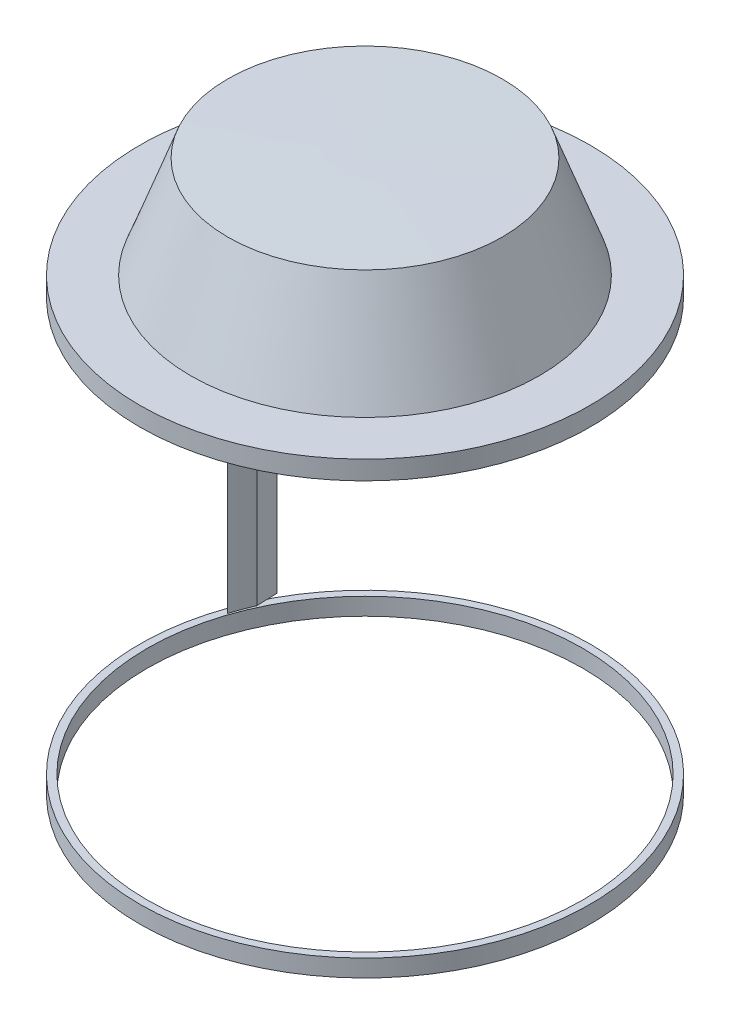
SolidWorks part; units mm, degrees
ref_plane "Alzado" through (0, 0, 0) normal (0, 0, 1) x (1, 0, 0)
ref_plane "Planta" through (0, 0, 0) normal (0, 1, 0) x (1, 0, 0)
ref_plane "Vista lateral" through (0, 0, 0) normal (1, 0, 0) x (0, 0, -1)
sketch "Croquis1" plane through (0, 0, 0) normal (0, 0, 1) x (1, 0, 0)
  line L0 (0, 38.8006) -> (0, -62.5731)
  line L1 (0, -62.5731) -> (50.8215, -62.5731)
  line L2 (50.8215, -62.5731) -> (50.8215, -58.6741)
  line L3 (50.8215, -58.6741) -> (46.9225, -58.6741)
  line L4 (46.9225, -58.6741) -> (46.9225, 34.5472)
  line L5 (46.9225, 34.5472) -> (50.8215, 34.5472)
  line L6 (50.8215, 34.5472) -> (50.8215, 38.8006)
  line L7 (50.8215, 38.8006) -> (0, 38.8006)
  dimension "D7" = 4.2534
  dimension "D1" = 101.3738
  dimension "D2" = 50.8215
  dimension "D3" = 3.899
  dimension "D4" = 3.899
  dimension "D5" = 93.2213
  dimension "D6" = 3.899
  dimension "D8" = 50.8215
revolve "Revolución1" add sketch "Croquis1" angle 360 about L0
ref_plane "Plano1" through (0, 0, 0) normal (0, 0, 1) x (1, 0, 0)
sketch "Croquis3" plane through (0, 0, 0) normal (0, 0, 1) x (1, 0, 0)
  line L0 (50.8215, -58.6741) -> (-50.8215, -58.6741) construction
  line L1 (-46.8969, 34.5263) -> (-44.3969, 34.5263)
  line L2 (-46.8969, 34.5263) -> (-46.8969, -58.6741)
  line L3 (-46.8969, -58.6741) -> (-44.3969, -58.6741)
  line L4 (-44.3969, 34.5263) -> (-44.3969, -58.6741)
  line L5 (-46.9225, 34.5472) -> (46.9225, 34.5472) construction
  line L6 (-41.3745, 34.5472) -> (-38.8745, 34.5472)
  line L7 (-41.3745, 34.5472) -> (-41.3745, -58.6741)
  line L8 (-41.3745, -58.6741) -> (-38.8745, -58.6741)
  line L9 (-38.8745, 34.5472) -> (-38.8745, -58.6741)
  dimension "D1" = 2.5
  dimension "D2" = 2.5
extrude "Saliente-Extruir1" add sketch "Croquis3" against normal blind 25 draft 1
sketch "Croquis5" plane through (0, 0, 0) normal (0, 0, 1) x (1, 0, 0)
  line L0 (0, 61.9733) -> (0, -94.3216) construction
  dimension "D1" = 156.2948
ref_plane "Plano2" through (0, 0, 0) normal (0, 0, 1) x (1, 0, 0)
sketch "Croquis6" plane through (0, 0, 0) normal (0, 0, 1) x (1, 0, 0)
  line L0 (37.4287, 61.7075) -> (37.4287, -71.7758) construction
  line L1 (-30.9408, 61.7075) -> (-30.9408, -75.0315) construction
  line L2 (0, 61.9733) -> (0, -94.3216) construction
  line L3 (0, 61.9733) -> (0, 38.8006)
  line L4 (50.8215, 38.8006) -> (-50.8215, 38.8006) construction
  line L5 (0, 38.8006) -> (-39.3097, 38.8006)
  line L6 (-39.3097, 38.8006) -> (-30.9408, 61.7075)
  line L7 (-30.9408, 61.7075) -> (0, 61.9733)
  dimension "D1" = 133.4833
  dimension "D2" = 136.739
revolve "Revolución3" add sketch "Croquis6" angle 360 about L3
ref_plane "Plano3" through (0, 60, 0) normal (0, 1, 0) x (1, 0, 0)
sketch "Croquis17" plane through (0, -62.5731, 0) normal (0, -1, 0) x (1, 0, 0)
  circle A0 centre (0, 0) radius 49.1543
extrude "Cortar-Extruir1" cut sketch "Croquis17" against normal blind 98
